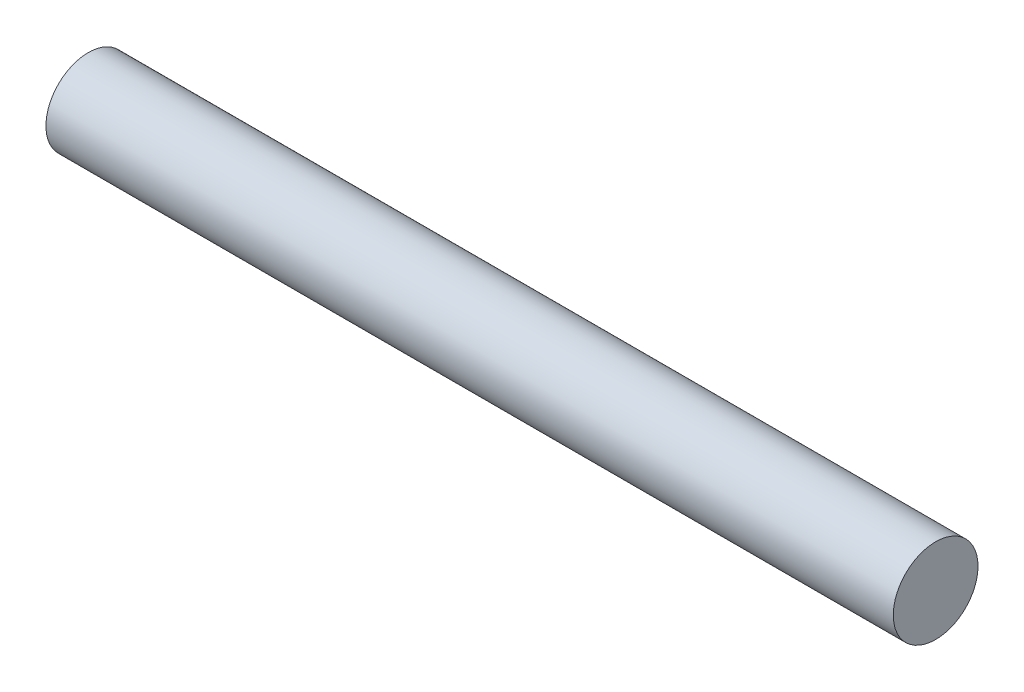
SolidWorks part; units mm, degrees
material "Plain Carbon Steel"
ref_plane "Front Plane" through (0, 0, 0) normal (0, 0, 1) x (1, 0, 0)
ref_plane "Top Plane" through (0, 0, 0) normal (0, 1, 0) x (1, 0, 0)
ref_plane "Right Plane" through (0, 0, 0) normal (1, 0, 0) x (0, 0, -1)
sketch "Sketch1" plane through (0, 0, 0) normal (1, 0, 0) x (0, 0, -1)
  circle A0 centre (0, 0) radius 9.525
extrude "Boss-Extrude1" add sketch "Sketch1" along normal blind 190.5
